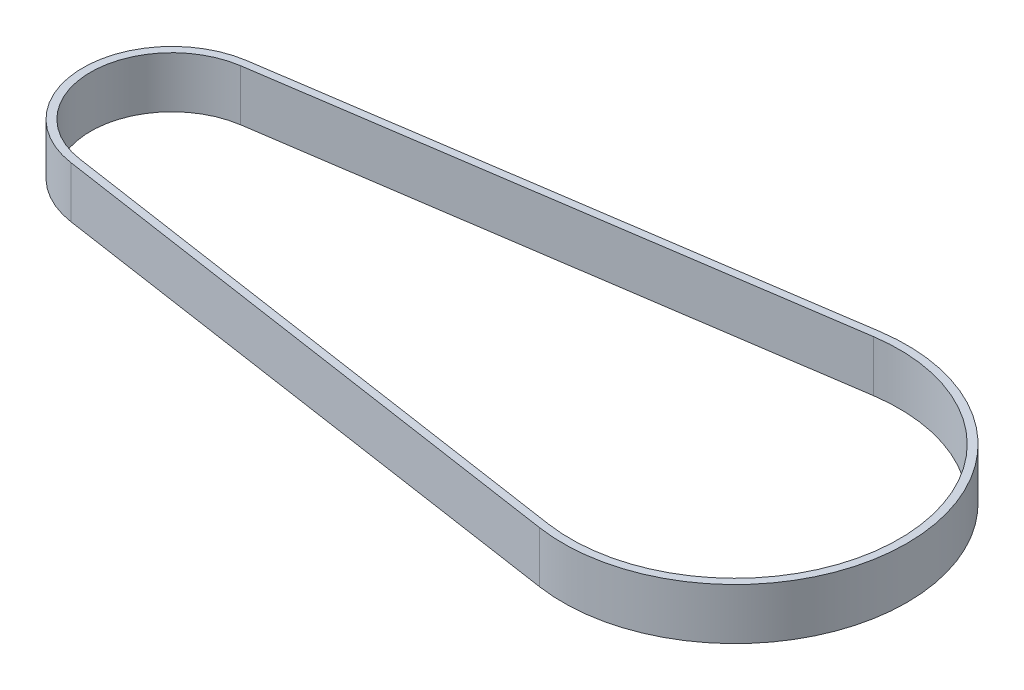
SolidWorks part; units mm, degrees
material "BUTYL"
ref_plane "Front Plane" through (0, 0, 0) normal (0, 0, 1) x (1, 0, 0)
ref_plane "Top Plane" through (0, 0, 0) normal (0, 1, 0) x (1, 0, 0)
ref_plane "Right Plane" through (0, 0, 0) normal (1, 0, 0) x (0, 0, -1)
sketch "Sketch1" plane through (0, 0, 0) normal (0, 1, 0) x (1, 0, 0)
  line L0 (-73.9541, 15.7421) -> (33.6689, 31.7364)
  line L1 (-73.9541, -15.7421) -> (33.6689, -31.7364)
  line L2 (-74.1746, -17.2258) -> (33.4484, -33.2201)
  line L3 (-74.1746, 17.2258) -> (33.4484, 33.2201)
  arc A0 (-73.9541, 15.7421) -> (-73.9541, -15.7421) centre (-71.6146, 0) ccw
  arc A1 (33.6689, -31.7364) -> (33.6689, 31.7364) centre (38.3854, 0) ccw
  arc A2 (-74.1746, 17.2258) -> (-74.1746, -17.2258) centre (-71.6146, 0) ccw
  arc A3 (33.4484, -33.2201) -> (33.4484, 33.2201) centre (38.3854, 0) ccw
  dimension "D1" = 31.83
  dimension "D2" = 64.17
  dimension "D3" = 110
  dimension "D4" = 1.5
extrude "Boss-Extrude1" add sketch "Sketch1" along normal blind 10
